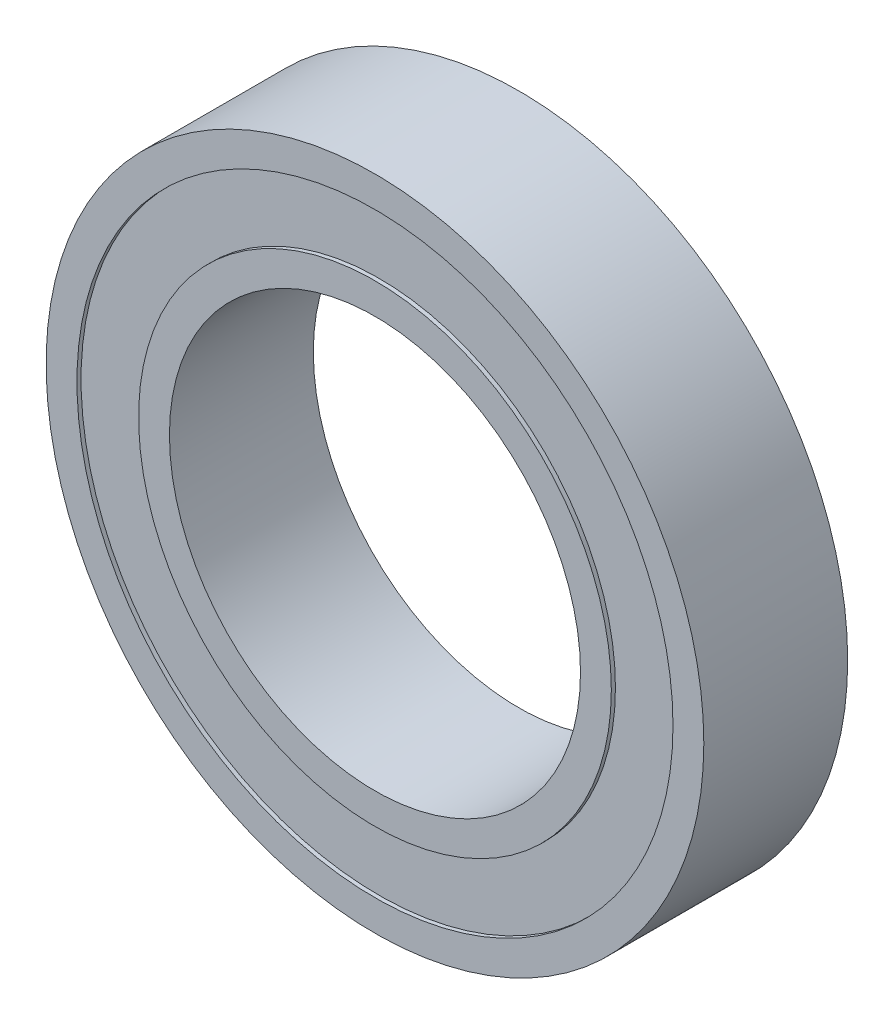
SolidWorks part; units mm, degrees
material "1023 Tôle d'acier au carbone (SS)"
ref_plane "Plan de face" through (0, 0, 0) normal (0, 0, 1) x (1, 0, 0)
ref_plane "Plan de dessus" through (0, 0, 0) normal (0, 1, 0) x (1, 0, 0)
ref_plane "Plan de droite" through (0, 0, 0) normal (1, 0, 0) x (0, 0, -1)
sketch "Esquisse1" plane through (0, 0, 0) normal (0, 0, 1) x (1, 0, 0)
  circle A0 centre (0, 0) radius 16
  circle A1 centre (0, 0) radius 10
  dimension "D1" = 20
  dimension "D2" = 32
extrude "Boss.-Extru.1" add sketch "Esquisse1" along normal blind 7
sketch "Esquisse2" plane through (0, 0, 7) normal (0, 0, 1) x (1, 0, 0)
  circle A0 centre (0, 0) radius 14.5
  circle A1 centre (0, 0) radius 11.5
  circle A2 centre (0, 0) radius 16 construction
  circle A3 centre (0, 0) radius 10 construction
  dimension "D1" = 1.5
  dimension "D2" = 1.5
extrude "Enlèv. mat.-Extru.1" cut sketch "Esquisse2" against normal blind 0.2
sketch "Esquisse3" plane through (0, 0, 0) normal (0, 0, -1) x (-1, 0, 0)
  circle A1 centre (0, 0) radius 11.5
  circle A2 centre (0, 0) radius 11.5
  circle A3 centre (0, 0) radius 14.5
  circle A4 centre (0, 0) radius 14.5
  dimension "D1" = 0
  dimension "D2" = 0
extrude "Enlèv. mat.-Extru.2" cut sketch "Esquisse3" against normal blind 0.2
